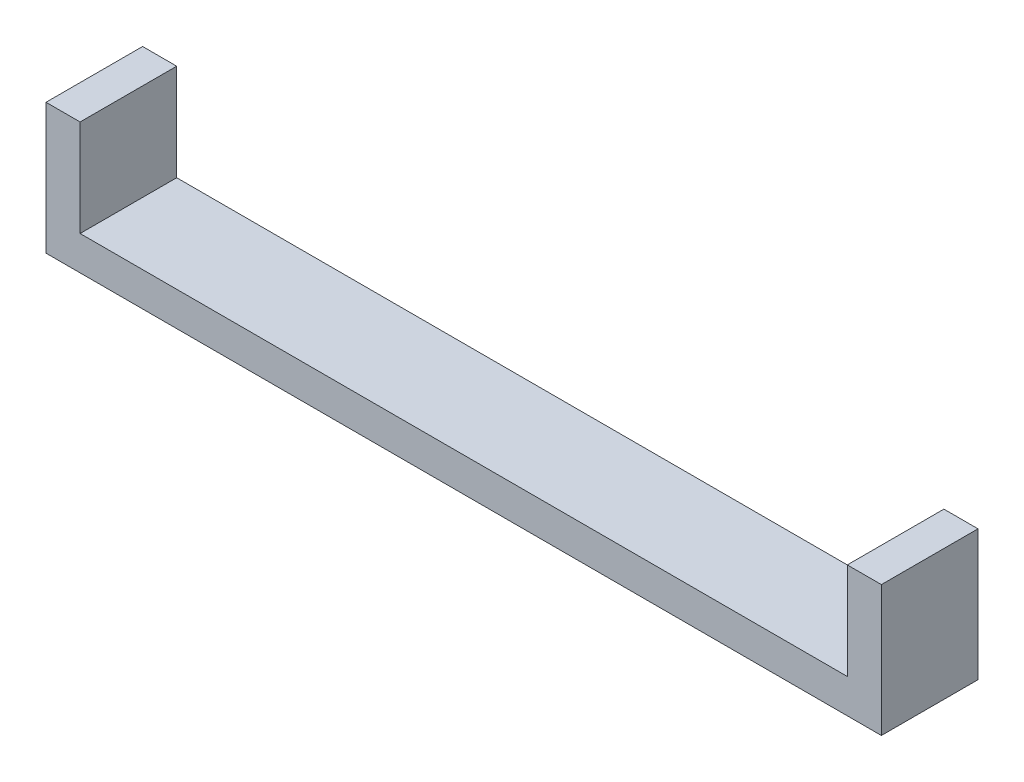
SolidWorks part; units mm, degrees
ref_plane "Front Plane" through (0, 0, 0) normal (0, 0, 1) x (1, 0, 0)
ref_plane "Top Plane" through (0, 0, 0) normal (0, 1, 0) x (1, 0, 0)
ref_plane "Right Plane" through (0, 0, 0) normal (1, 0, 0) x (0, 0, -1)
sketch "Sketch1" plane through (0, 0, 0) normal (1, 0, 0) x (0, 0, -1)
  line L0 (0, 0) -> (1.6017, 0) construction
  line L1 (1.5877, 2.75) -> (-1.5877, 2.75)
  line L2 (-1.5877, 2.75) -> (-3.1754, 0)
  line L3 (-3.1754, 0) -> (-1.5877, -2.75)
  line L4 (-1.5877, -2.75) -> (1.5877, -2.75)
  line L5 (1.5877, -2.75) -> (3.1754, 0)
  line L6 (3.1754, 0) -> (1.5877, 2.75)
  line L8 (-4.25, -4.25) -> (4.25, -4.25)
  line L9 (-4.25, -4.25) -> (-4.25, 4.25)
  line L10 (-4.25, 4.25) -> (4.25, 4.25)
  line L11 (4.25, -4.25) -> (4.25, 4.25)
  line L12 (-4.25, -4.25) -> (4.25, 4.25) construction
  line L13 (-4.25, 4.25) -> (4.25, -4.25) construction
  circle A0 centre (0, 0) radius 2.75 construction
  dimension "D1" = 5.5
  dimension "D2" = 8.5
  dimension "D3" = 8.5
extrude "Boss-Extrude1" add sketch "Sketch1" along normal blind 5
sketch "Sketch2" plane through (0, 0, 0) normal (-1, 0, 0) x (0, 0, 1)
  line L1 (-4.25, -4.25) -> (4.25, -4.25)
  line L2 (-4.25, -4.25) -> (-4.25, 4.25)
  line L3 (-4.25, 4.25) -> (4.25, 4.25)
  line L4 (4.25, -4.25) -> (4.25, 4.25)
  line L5 (-4.25, -4.25) -> (4.25, 4.25) construction
  line L6 (-4.25, 4.25) -> (4.25, -4.25) construction
  point P0 (0, 0)
extrude "Boss-Extrude2" add sketch "Sketch2" along normal blind 2
sketch "Sketch3" plane through (0, 0, 0) normal (1, 0, 0) x (0, 0, -1)
  circle A0 centre (0, 0) radius 1.5
  dimension "D1" = 3
extrude "Cut-Extrude1" cut sketch "Sketch3" against normal blind 2
sketch "Sketch4" plane through (0, -4.25, 0) normal (0, -1, 0) x (1, 0, 0)
  line L0 (5, -4.25) -> (-2, -4.25) construction
  line L1 (-2, 4.25) -> (79.5, 4.25)
  line L2 (-2, 4.25) -> (-2, -4.25)
  line L3 (-2, -4.25) -> (79.5, -4.25)
  line L4 (79.5, 4.25) -> (79.5, -4.25)
  dimension "D1" = 81.5
extrude "Boss-Extrude3" add sketch "Sketch4" along normal blind 3
sketch "Sketch5" plane through (0, -4.25, 0) normal (0, 1, 0) x (1, 0, 0)
  line L0 (79.5, -4.25) -> (5, -4.25) construction
  line L1 (79.5, 4.25) -> (72.5, 4.25)
  line L2 (79.5, 4.25) -> (79.5, -4.25)
  line L3 (79.5, -4.25) -> (72.5, -4.25)
  line L4 (72.5, 4.25) -> (72.5, -4.25)
  dimension "D1" = 7
extrude "Boss-Extrude4" add sketch "Sketch5" along normal up to surface (8.5 mm away) up to face at (1.5, 4.25, 0)
sketch "Sketch6" plane through (72.5, 0, 0) normal (-1, 0, 0) x (0, 0, 1)
  line L0 (-4.25, -4.25) -> (4.25, -4.25) construction
  line L1 (3.1754, 0) -> (1.5877, 2.75)
  line L2 (1.5877, 2.75) -> (-1.5877, 2.75)
  line L3 (-1.5877, 2.75) -> (-3.1754, 0)
  line L4 (-3.1754, 0) -> (-1.5877, -2.75)
  line L5 (-1.5877, -2.75) -> (1.5877, -2.75)
  line L6 (1.5877, -2.75) -> (3.1754, 0)
  circle A0 centre (0, 0) radius 2.75 construction
  dimension "D1" = 5.5
extrude "Cut-Extrude2" cut sketch "Sketch6" against normal blind 5
sketch "Sketch7" plane through (77.5, 0, 0) normal (-1, 0, 0) x (0, 0, 1)
  circle A0 centre (0, 0) radius 1.5
  dimension "D1" = 3
extrude "Cut-Extrude3" cut sketch "Sketch7" against normal blind 5
sketch "Sketch8" plane through (-2, 0, 0) normal (-1, 0, 0) x (0, 0, 1)
  line L0 (-1.5877, 2.75) -> (1.5877, 2.75) construction
  line L1 (1.5877, 2.75) -> (3.1754, 0) construction
  line L2 (3.1754, 0) -> (1.5877, -2.75) construction
  line L3 (1.5877, -2.75) -> (-1.5877, -2.75) construction
  line L4 (-1.5877, -2.75) -> (-3.1754, 0) construction
  line L5 (-3.1754, 0) -> (-1.5877, 2.75) construction
  line L6 (-1.5877, 2.75) -> (1.5877, 2.75)
  line L7 (1.5877, 2.75) -> (3.1754, 0)
  line L8 (3.1754, 0) -> (1.5877, -2.75)
  line L9 (1.5877, -2.75) -> (-1.5877, -2.75)
  line L10 (-1.5877, -2.75) -> (-3.1754, 0)
  line L11 (-3.1754, 0) -> (-1.5877, 2.75)
extrude "Cut-Extrude4" cut sketch "Sketch8" against normal blind 10
sketch "Sketch9" plane through (5, 0, 0) normal (1, 0, 0) x (0, 0, -1)
  line L1 (-4.25, 4.25) -> (4.25, 4.25)
  line L2 (-4.25, 4.25) -> (-4.25, -4.25)
  line L3 (-4.25, -4.25) -> (4.25, -4.25)
  line L4 (4.25, 4.25) -> (4.25, -4.25)
  circle A0 centre (0, 0) radius 1.5
  dimension "D1" = 3
extrude "Boss-Extrude5" add sketch "Sketch9" against normal blind 2
sketch "Sketch10" plane through (79.5, 0, 0) normal (1, 0, 0) x (0, 0, -1)
  line L0 (-3.1754, 0) -> (-1.5877, 2.75) construction
  line L1 (-1.5877, -2.75) -> (-3.1754, 0) construction
  line L2 (1.5877, -2.75) -> (-1.5877, -2.75) construction
  line L3 (3.1754, 0) -> (1.5877, -2.75) construction
  line L4 (1.5877, 2.75) -> (3.1754, 0) construction
  line L5 (-1.5877, 2.75) -> (1.5877, 2.75) construction
  line L6 (-3.1754, 0) -> (-1.5877, 2.75)
  line L7 (-1.5877, -2.75) -> (-3.1754, 0)
  line L8 (1.5877, -2.75) -> (-1.5877, -2.75)
  line L9 (3.1754, 0) -> (1.5877, -2.75)
  line L10 (1.5877, 2.75) -> (3.1754, 0)
  line L11 (-1.5877, 2.75) -> (1.5877, 2.75)
extrude "Cut-Extrude5" cut sketch "Sketch10" against normal blind 2
sketch "Sketch11" plane through (72.5, 0, 0) normal (-1, 0, 0) x (0, 0, 1)
  line L1 (-4.25, 4.25) -> (4.25, 4.25)
  line L2 (-4.25, 4.25) -> (-4.25, -4.25)
  line L3 (-4.25, -4.25) -> (4.25, -4.25)
  line L4 (4.25, 4.25) -> (4.25, -4.25)
  circle A0 centre (0, 0) radius 1.5
  dimension "D1" = 3
extrude "Boss-Extrude6" add sketch "Sketch11" against normal blind 2
sketch "Sketch12" plane through (3, 0, 0) normal (-1, 0, 0) x (0, 0, 1)
  line L0 (-3.1754, 0) -> (-1.5877, 2.75) construction
  line L1 (-1.5877, -2.75) -> (-3.1754, 0) construction
  line L2 (-1.5877, -2.75) -> (1.5877, -2.75) construction
  line L3 (1.5877, -2.75) -> (3.1754, 0) construction
  line L4 (3.1754, 0) -> (1.5877, 2.75) construction
  line L5 (-1.5877, 2.75) -> (1.5877, 2.75) construction
  line L6 (-3.1754, 0) -> (-1.5877, 2.75)
  line L7 (-1.5877, -2.75) -> (-3.1754, 0)
  line L8 (-1.5877, -2.75) -> (1.5877, -2.75)
  line L9 (1.5877, -2.75) -> (3.1754, 0)
  line L10 (3.1754, 0) -> (1.5877, 2.75)
  line L11 (-1.5877, 2.75) -> (1.5877, 2.75)
extrude "Boss-Extrude7" add sketch "Sketch12" along normal up to surface (5 mm away)
sketch "Sketch13" plane through (74.5, 0, 0) normal (1, 0, 0) x (0, 0, -1)
  line L0 (-1.5877, 2.75) -> (-3.1754, 0) construction
  line L1 (-3.1754, 0) -> (-1.5877, -2.75) construction
  line L2 (-1.5877, -2.75) -> (1.5877, -2.75) construction
  line L3 (1.5877, -2.75) -> (3.1754, 0) construction
  line L4 (3.1754, 0) -> (1.5877, 2.75) construction
  line L5 (1.5877, 2.75) -> (-1.5877, 2.75) construction
  line L6 (-1.5877, 2.75) -> (-3.1754, 0)
  line L7 (-3.1754, 0) -> (-1.5877, -2.75)
  line L8 (-1.5877, -2.75) -> (1.5877, -2.75)
  line L9 (1.5877, -2.75) -> (3.1754, 0)
  line L10 (3.1754, 0) -> (1.5877, 2.75)
  line L11 (1.5877, 2.75) -> (-1.5877, 2.75)
extrude "Boss-Extrude8" add sketch "Sketch13" along normal up to surface (5 mm away) up to face at (79.5, 0, 0)
sketch "Sketch14" plane through (-2, 0, 0) normal (-1, 0, 0) x (0, 0, 1)
  line L1 (-4.25, 4.25) -> (4.25, 4.25)
  line L2 (-4.25, 4.25) -> (-4.25, -7.25)
  line L3 (-4.25, -7.25) -> (4.25, -7.25)
  line L4 (4.25, 4.25) -> (4.25, -7.25)
extrude "Cut-Extrude6" cut sketch "Sketch14" against normal blind 4
sketch "Sketch15" plane through (79.5, 0, 0) normal (1, 0, 0) x (0, 0, -1)
  line L1 (-4.25, 4.25) -> (4.25, 4.25)
  line L2 (-4.25, 4.25) -> (-4.25, -7.25)
  line L3 (-4.25, -7.25) -> (4.25, -7.25)
  line L4 (4.25, 4.25) -> (4.25, -7.25)
extrude "Cut-Extrude7" cut sketch "Sketch15" against normal blind 4
sketch "Sketch16" plane through (5, 0, 0) normal (1, 0, 0) x (0, 0, -1)
  circle A0 centre (0, 0) radius 1.5
extrude "Cut-Extrude8" cut sketch "Sketch16" against normal blind 4
sketch "Sketch17" plane through (74.5, 0, 0) normal (-1, 0, 0) x (0, 0, 1)
  circle A0 centre (0, 0) radius 1.5
extrude "Cut-Extrude9" cut sketch "Sketch17" against normal blind 4
sketch "Sketch19" plane through (5, 0, 0) normal (1, 0, 0) x (0, 0, -1)
  line L1 (-4.25, 4.25) -> (4.25, 4.25)
  line L2 (-4.25, 4.25) -> (-4.25, -4.25)
  line L3 (-4.25, -4.25) -> (4.25, -4.25)
  line L4 (4.25, 4.25) -> (4.25, -4.25)
extrude "Boss-Extrude9" add sketch "Sketch19" against normal up to surface (3 mm away) up to face at (2, 0, 1.5)
sketch "Sketch20" plane through (72.5, 0, 0) normal (-1, 0, 0) x (0, 0, 1)
  line L1 (-4.25, 4.25) -> (4.25, 4.25)
  line L2 (-4.25, 4.25) -> (-4.25, -4.25)
  line L3 (-4.25, -4.25) -> (4.25, -4.25)
  line L4 (4.25, 4.25) -> (4.25, -4.25)
extrude "Boss-Extrude10" add sketch "Sketch20" against normal up to surface (3 mm away) up to face at (75.5, 0, -1.5)
